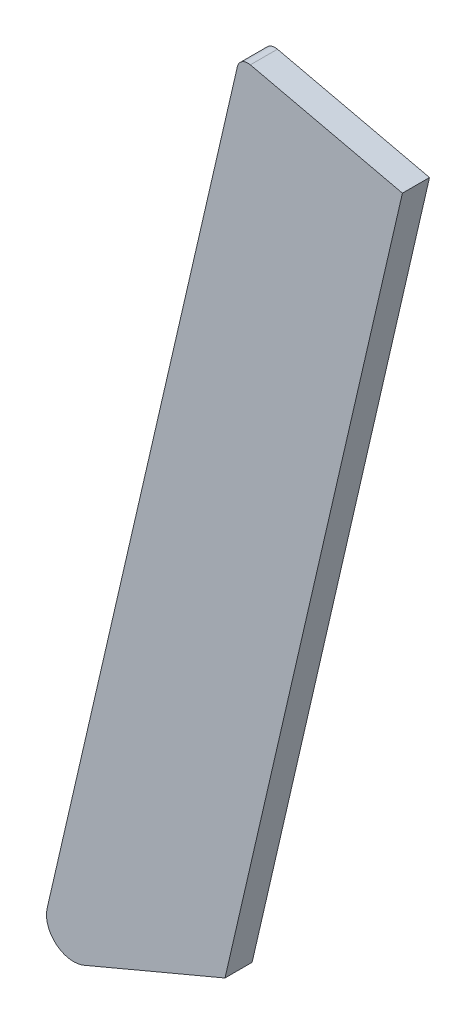
SolidWorks part; units mm, degrees
material "Nylon 101"
ref_plane "Front Plane" through (0, 0, 0) normal (0, 0, 1) x (1, 0, 0)
ref_plane "Top Plane" through (0, 0, 0) normal (0, 1, 0) x (1, 0, 0)
ref_plane "Right Plane" through (0, 0, 0) normal (1, 0, 0) x (0, 0, -1)
sketch "Sketch1" plane through (0, 0, 0) normal (0, 0, 1) x (1, 0, 0)
  line L4 (-41.0003, -26.2879) -> (-63.2873, -122.8234)
  line L5 (-58.96, -126.4631) -> (-42.4476, -119.4999)
  line L6 (-42.4476, -119.4999) -> (-21.6579, -29.45)
  line L7 (-21.6579, -29.45) -> (-39.4772, -25.3361)
  line L8 (-41.0003, -26.2879) -> (-63.2873, -122.8234)
  line L9 (-58.96, -126.4631) -> (-42.4476, -119.4999)
  line L10 (-42.4476, -119.4999) -> (-21.6579, -29.45)
  line L11 (-21.6579, -29.45) -> (-39.4772, -25.3361)
  arc A2 (-63.2873, -122.8234) -> (-58.96, -126.4631) centre (-60.1937, -123.5376) ccw
  arc A3 (-39.4772, -25.3361) -> (-41.0003, -26.2879) centre (-39.7629, -26.5735) ccw
  arc A4 (-63.2873, -122.8234) -> (-58.96, -126.4631) centre (-60.1937, -123.5376) ccw
  arc A5 (-39.4772, -25.3361) -> (-41.0003, -26.2879) centre (-39.7629, -26.5735) ccw
  dimension "D1" = 0
extrude "Boss-Extrude1" add sketch "Sketch1" along normal blind 3.175
